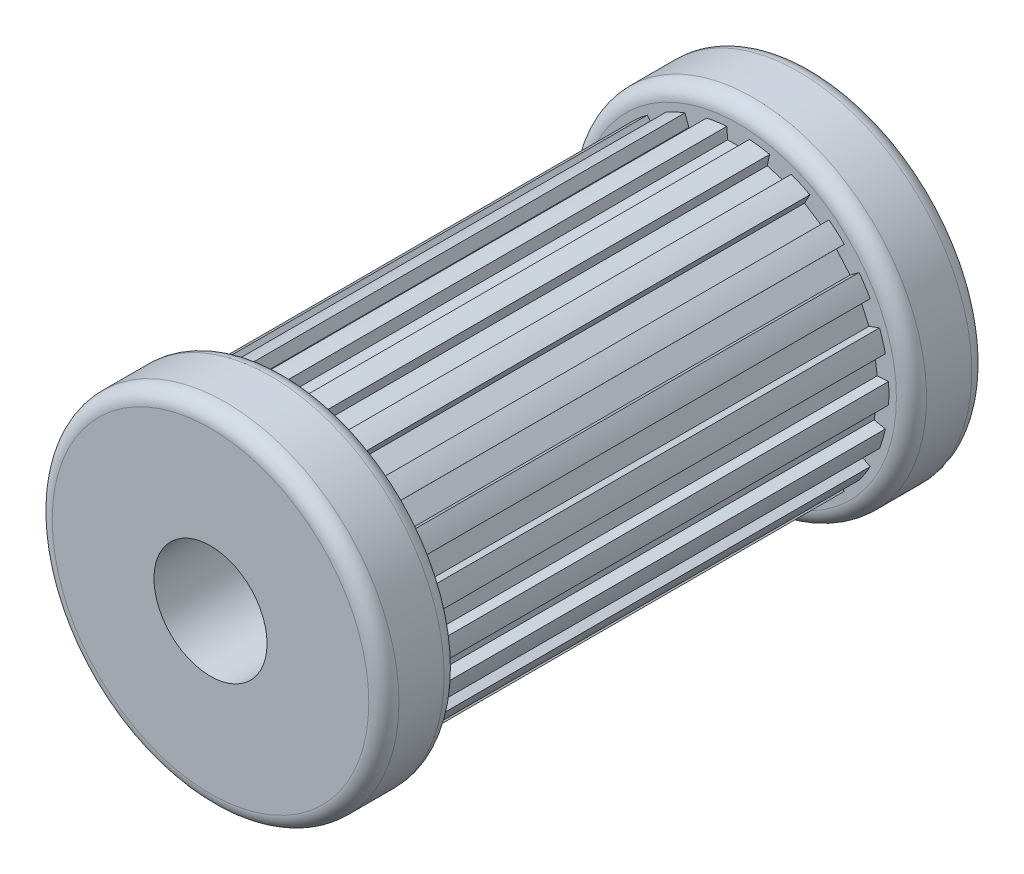
SolidWorks part; units mm, degrees
ref_plane "Front Plane" through (0, 0, 0) normal (0, 0, 1) x (1, 0, 0)
ref_plane "Top Plane" through (0, 0, 0) normal (0, 1, 0) x (1, 0, 0)
ref_plane "Right Plane" through (0, 0, 0) normal (1, 0, 0) x (0, 0, -1)
sketch "Sketch1" plane through (0, 0, 0) normal (0, 0, 1) x (1, 0, 0)
  circle A0 centre (0, 0) radius 20
  dimension "D1" = 40
extrude "Boss-Extrude1" add sketch "Sketch1" along normal blind 70
sketch "Sketch2" plane through (0, 0, 70) normal (0, 0, 1) x (1, 0, 0)
  line L0 (-1.3875, 18.4479) -> (1.3875, 18.4479)
  line L1 (1.3875, 18.4479) -> (1.5, 19.9437)
  line L2 (-1.3875, 18.4479) -> (-1.5, 19.9437)
  circle A0 centre (0, 0) radius 20 construction
  arc A1 (1.5, 19.9437) -> (-1.5, 19.9437) centre (0, 0) ccw
  point P2 (0, 18.4479)
  dimension "D1" = 1.5
  dimension "D2" = 3
extrude "Cut-Extrude1" cut sketch "Sketch2" against normal through all
pattern_circular "CirPattern1" count 22 over 360 about axis through (0, 0, 0) along (0, 0, 1) of "Cut-Extrude1"
sketch "Sketch3" plane through (0, 0, 70) normal (0, 0, 1) x (1, 0, 0)
  circle A0 centre (0, 0) radius 23
  dimension "D1" = 46
extrude "Boss-Extrude2" add sketch "Sketch3" against normal blind 10
sketch "Sketch5" plane through (0, 0, 0) normal (0, 0, -1) x (-1, 0, 0)
  circle A0 centre (0, 0) radius 23
extrude "Boss-Extrude3" add sketch "Sketch5" along normal blind 10
sketch "Sketch6" plane through (0, 0, 70) normal (0, 0, 1) x (1, 0, 0)
  circle A0 centre (0, 0) radius 7.5
  dimension "D1" = 15
extrude "Cut-Extrude2" cut sketch "Sketch6" against normal through all
fillet "Fillet1" radius 2 4 edges at (23, 0, 60) (-23, 0, 0) (-23, 0, -10) (23, 0, 70)
